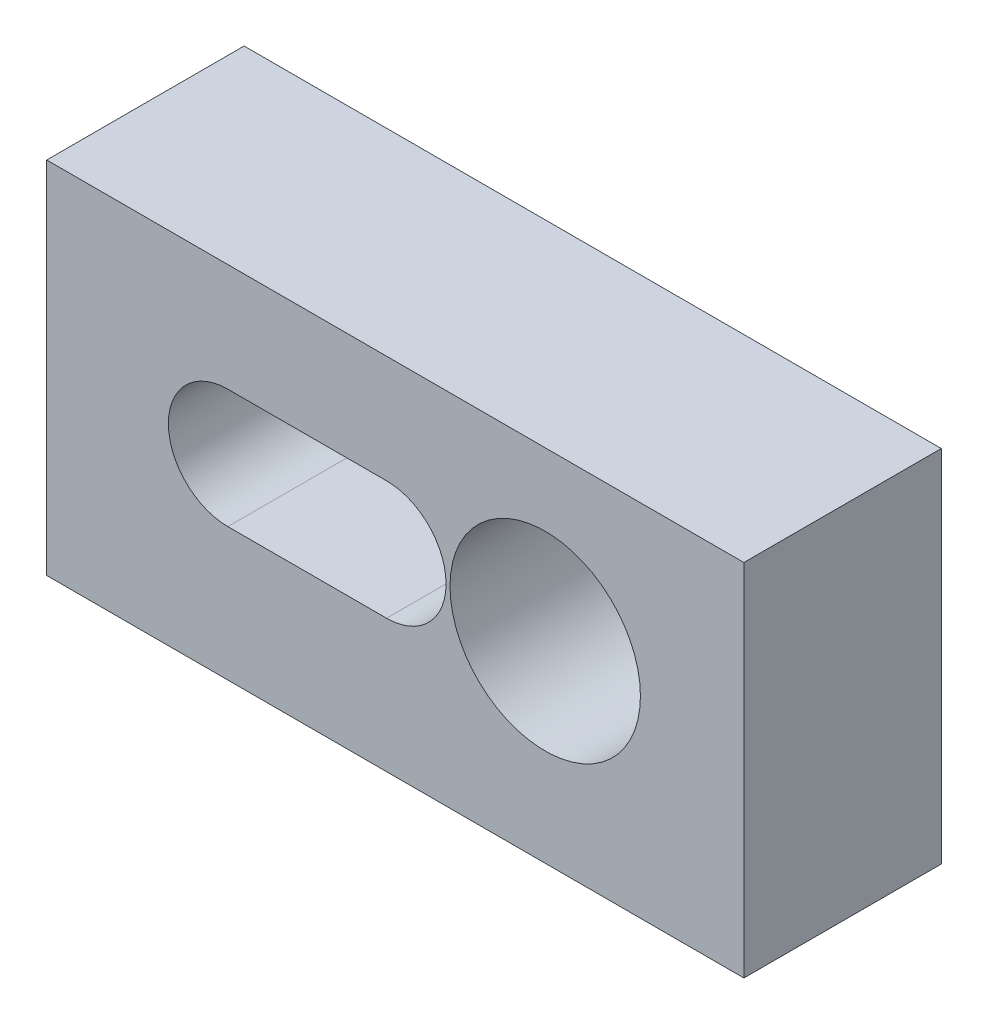
SolidWorks part; units mm, degrees
ref_plane "Front Plane" through (0, 0, 0) normal (0, 0, 1) x (1, 0, 0)
ref_plane "Top Plane" through (0, 0, 0) normal (0, 1, 0) x (1, 0, 0)
ref_plane "Right Plane" through (0, 0, 0) normal (1, 0, 0) x (0, 0, -1)
sketch "Sketch1" plane through (0, 0, 0) normal (0, 1, 0) x (1, 0, 0)
  line L1 (-39.0999, 16.0935) -> (16.7001, 16.0935)
  line L2 (-39.0999, 16.0935) -> (-39.0999, 0.2935)
  line L3 (-39.0999, 0.2935) -> (16.7001, 0.2935)
  line L4 (16.7001, 16.0935) -> (16.7001, 0.2935)
  dimension "D1" = 55.8
  dimension "D2" = 15.8
extrude "Boss-Extrude1" add sketch "Sketch1" along normal blind 28.8
sketch "Sketch2" plane through (0, 0, -0.2935) normal (0, 0, 1) x (1, 0, 0)
  line L0 (-39.0999, 0) -> (16.7001, 0) construction
  line L1 (-11.8999, 15.4) -> (-24.5999, 15.4) construction
  line L2 (-11.8999, 10.6375) -> (-24.5999, 10.6375)
  line L3 (-11.8999, 20.1625) -> (-24.5999, 20.1625)
  line L4 (16.7001, 28.8) -> (16.7001, 0) construction
  circle A0 centre (0.8001, 15.4) radius 7.62
  arc A1 (-11.8999, 10.6375) -> (-11.8999, 20.1625) centre (-11.8999, 15.4) ccw
  arc A2 (-24.5999, 20.1625) -> (-24.5999, 10.6375) centre (-24.5999, 15.4) ccw
  point P6 (-18.2499, 15.4)
  dimension "D4" = 15.24
  dimension "D5" = 4.7625
  dimension "D1" = 15.4
  dimension "D2" = 12.7
  dimension "D3" = 12.7
  dimension "D6" = 15.9
extrude "Cut-Extrude1" cut sketch "Sketch2" against normal blind 12.7
sketch "Sketch4" plane through (0, 0, -16.0935) normal (0, 0, -1) x (-1, 0, 0)
  line L0 (-16.7001, 28.8) -> (-16.7001, 0) construction
  line L1 (-16.7001, 0) -> (39.0999, 0) construction
  circle A6 centre (-0.8001, 15.4) radius 2.7781
  circle A7 centre (11.8999, 15.4) radius 1.8415
  circle A8 centre (24.5999, 15.4) radius 1.8415
  dimension "D1" = 5.5563
  dimension "D2" = 3.683
  dimension "D3" = 3.683
  dimension "D4" = 12.7
  dimension "D5" = 12.7
  dimension "D6" = 15.9
  dimension "D7" = 15.4
extrude "Cut-Extrude2" cut sketch "Sketch4" against normal blind 12.7
sketch "Sketch5" plane through (0, 0, -16.0935) normal (0, 0, -1) x (-1, 0, 0)
  line L2 (24.5999, 20.1625) -> (11.8999, 20.1625)
  line L3 (11.8999, 10.6375) -> (24.5999, 10.6375)
  line L12 (24.5999, 20.1625) -> (11.8999, 20.1625)
  line L13 (11.8999, 10.6375) -> (24.5999, 10.6375)
  arc A2 (11.8999, 20.1625) -> (11.8999, 10.6375) centre (11.8999, 15.4) ccw
  arc A3 (24.5999, 10.6375) -> (24.5999, 20.1625) centre (24.5999, 15.4) ccw
  arc A4 (11.8999, 20.1625) -> (11.8999, 10.6375) centre (11.8999, 15.4) ccw
  arc A5 (24.5999, 10.6375) -> (24.5999, 20.1625) centre (24.5999, 15.4) ccw
  dimension "D2" = 0
extrude "Cut-Extrude6" cut sketch "Sketch5" against normal blind 1.905
sketch "Sketch6" plane through (0, 28.8, 0) normal (0, 1, 0) x (1, 0, 0)
  text T0 "TOP\r\n"
